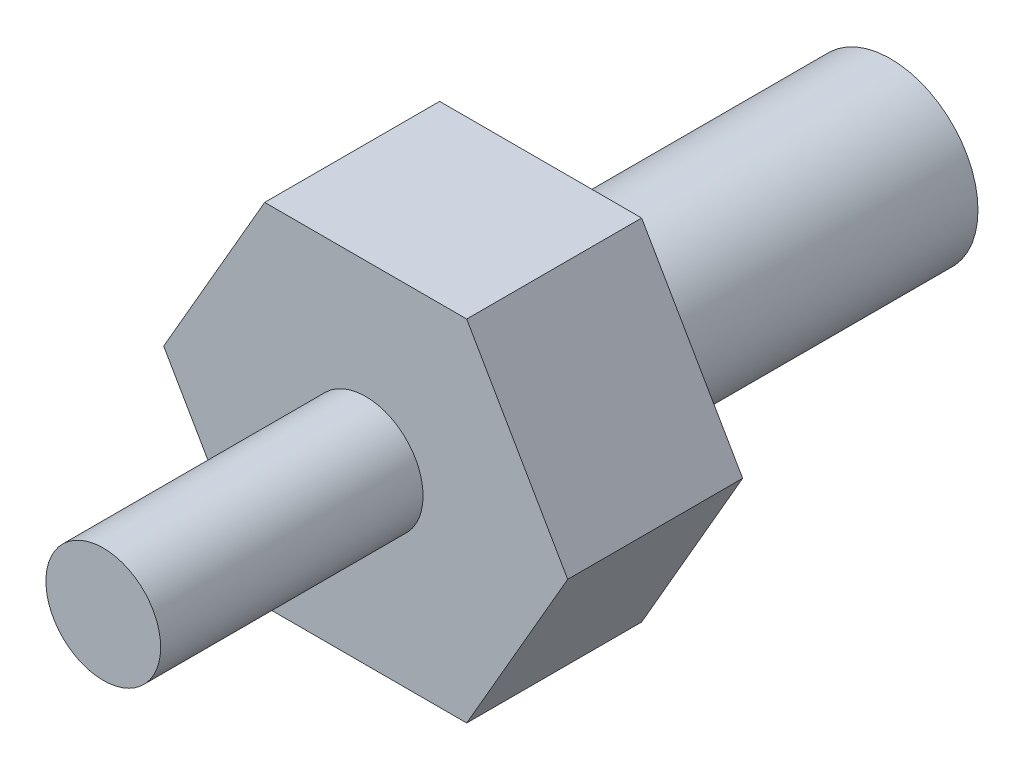
SolidWorks part; units mm, degrees
ref_plane "Front Plane" through (0, 0, 0) normal (0, 0, 1) x (1, 0, 0)
ref_plane "Top Plane" through (0, 0, 0) normal (0, 1, 0) x (1, 0, 0)
ref_plane "Right Plane" through (0, 0, 0) normal (1, 0, 0) x (0, 0, -1)
sketch "Sketch1" plane through (0, 0, 0) normal (0, 0, 1) x (1, 0, 0)
  circle A0 centre (0, 0) radius 3.175
extrude "Boss-Extrude1" add sketch "Sketch1" along normal blind 12.7
sketch "Sketch2" plane through (0, 0, 12.7) normal (0, 0, 1) x (1, 0, 0)
  line L1 (3.6662, -6.35) -> (7.3323, 0)
  line L2 (7.3323, 0) -> (3.6662, 6.35)
  line L3 (3.6662, 6.35) -> (-3.6662, 6.35)
  line L4 (-3.6662, 6.35) -> (-7.3323, 0)
  line L5 (-7.3323, 0) -> (-3.6662, -6.35)
  line L6 (-3.6662, -6.35) -> (3.6662, -6.35)
  circle A0 centre (0, 0) radius 6.35 construction
  dimension "D1" = 12.7
extrude "Boss-Extrude2" add sketch "Sketch2" along normal blind 6.35
sketch "Sketch3" plane through (0, 0, 19.05) normal (0, 0, 1) x (1, 0, 0)
  circle A0 centre (0, 0) radius 2.0828
extrude "Boss-Extrude3" add sketch "Sketch3" along normal blind 9.525
